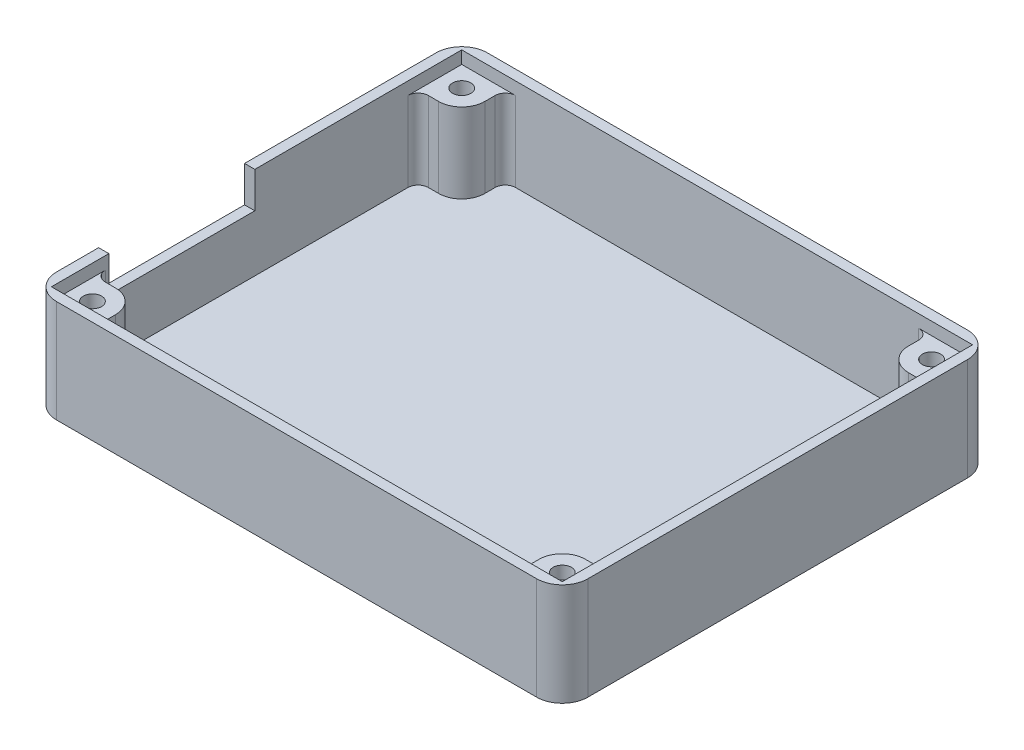
SolidWorks part; units mm, degrees
ref_plane "Front Plane" through (0, 0, 0) normal (0, 0, 1) x (1, 0, 0)
ref_plane "Top Plane" through (0, 0, 0) normal (0, 1, 0) x (1, 0, 0)
ref_plane "Right Plane" through (0, 0, 0) normal (1, 0, 0) x (0, 0, -1)
sketch "Sketch1" plane through (0, 0, 0) normal (0, 1, 0) x (1, 0, 0)
  line L0 (-36.1611, 34.3606) -> (-36.1611, -16.4394) construction
  line L1 (-38.7011, 34.3606) -> (24.5449, 34.3606)
  line L2 (-38.7011, 34.3606) -> (-38.7011, -16.4394)
  line L3 (-38.7011, -16.4394) -> (24.5449, -16.4394)
  line L4 (24.5449, 34.3606) -> (24.5449, -16.4394)
  line L5 (-38.7011, 31.8206) -> (24.5449, 31.8206) construction
  line L6 (22.0049, 34.3606) -> (22.0049, -16.4394) construction
  line L7 (-38.7011, -13.8994) -> (24.5449, -13.8994) construction
  line L8 (-7.0781, 31.8206) -> (-7.0781, -13.8994) construction
  line L9 (22.0049, 8.9606) -> (-36.1611, 8.9606) construction
  dimension "D1" = 63.246
  dimension "D2" = 50.8
  dimension "D3" = 2.54
  dimension "D4" = 2.54
  dimension "D5" = 2.54
  dimension "D6" = 2.54
sketch "Sketch4" plane through (0, 0, 0) normal (0, 1, 0) x (1, 0, 0)
  line L0 (-34.6003, 169.5077) -> (28.6457, 169.5077) construction
  dimension "D1" = 63.246
sketch "Sketch5" plane through (0, 0, 0) normal (0, 1, 0) x (1, 0, 0)
  line L8 (25.8149, -17.7094) -> (25.8149, 35.6306)
  line L9 (25.8149, 35.6306) -> (-39.9711, 35.6306)
  line L10 (-39.9711, 35.6306) -> (-39.9711, -17.7094)
  line L11 (-39.9711, -17.7094) -> (25.8149, -17.7094)
  line L12 (25.8149, -17.7094) -> (25.8149, 35.6306)
  line L13 (25.8149, 35.6306) -> (-39.9711, 35.6306)
  line L14 (-39.9711, 35.6306) -> (-39.9711, -17.7094)
  line L15 (-39.9711, -17.7094) -> (25.8149, -17.7094)
  dimension "D1" = 1.27
extrude "Boss-Extrude1" add sketch "Sketch5" along normal blind 12.7
sketch "Sketch7" plane through (0, 0, 0) normal (0, -1, 0) x (1, 0, 0)
  line L0 (-38.7011, -34.3606) -> (24.5449, -34.3606) construction
  line L1 (-38.7011, -34.3606) -> (-38.7011, 16.4394) construction
  line L2 (-38.7011, 16.4394) -> (24.5449, 16.4394) construction
  line L3 (24.5449, -34.3606) -> (24.5449, 16.4394) construction
  line L4 (-32.0336, -34.3606) -> (17.8774, -34.3606)
  line L5 (-38.7011, -27.6931) -> (-38.7011, 9.7719)
  line L6 (-32.0336, 16.4394) -> (17.8774, 16.4394)
  line L7 (24.5449, -27.6931) -> (24.5449, 9.7719)
  line L8 (-33.3036, 13.8994) -> (-33.3036, 15.1694)
  line L9 (-36.1611, 11.0419) -> (-37.4311, 11.0419)
  line L10 (-36.1611, -34.3606) -> (-36.1611, 16.4394) construction
  line L11 (-38.7011, 13.8994) -> (24.5449, 13.8994) construction
  line L12 (-38.7011, 13.8994) -> (24.5449, 13.8994) construction
  line L13 (-36.1611, -34.3606) -> (-36.1611, 16.4394) construction
  line L14 (-7.0781, 13.8994) -> (-7.0781, -34.3606) construction
  line L15 (19.1474, 13.8994) -> (19.1474, 15.1694)
  line L16 (22.0049, 11.0419) -> (23.2749, 11.0419)
  line L17 (-36.1611, -8.9606) -> (22.5409, -8.9606) construction
  line L18 (22.0049, -28.9631) -> (23.2749, -28.9631)
  line L19 (19.1474, -31.8206) -> (19.1474, -33.0906)
  line L20 (-33.3036, -31.8206) -> (-33.3036, -33.0906)
  line L21 (-36.1611, -28.9631) -> (-37.4311, -28.9631)
  circle A0 centre (-36.1611, 13.8994) radius 1.5875 construction
  arc A1 (-36.1611, 11.0419) -> (-33.3036, 13.8994) centre (-36.1611, 13.8994) ccw
  arc A2 (-38.7011, 9.7719) -> (-37.4311, 11.0419) centre (-37.4311, 9.7719) cw
  circle A3 centre (-36.1611, 13.8994) radius 2.8575 construction
  arc A4 (-33.3036, 15.1694) -> (-32.0336, 16.4394) centre (-32.0336, 15.1694) cw
  arc A5 (19.1474, 15.1694) -> (17.8774, 16.4394) centre (17.8774, 15.1694) ccw
  arc A6 (22.0049, 11.0419) -> (19.1474, 13.8994) centre (22.0049, 13.8994) cw
  arc A7 (24.5449, 9.7719) -> (23.2749, 11.0419) centre (23.2749, 9.7719) ccw
  arc A8 (24.5449, -27.6931) -> (23.2749, -28.9631) centre (23.2749, -27.6931) cw
  arc A9 (22.0049, -28.9631) -> (19.1474, -31.8206) centre (22.0049, -31.8206) ccw
  arc A10 (19.1474, -33.0906) -> (17.8774, -34.3606) centre (17.8774, -33.0906) cw
  arc A11 (-33.3036, -33.0906) -> (-32.0336, -34.3606) centre (-32.0336, -33.0906) ccw
  arc A12 (-36.1611, -28.9631) -> (-33.3036, -31.8206) centre (-36.1611, -31.8206) cw
  arc A13 (-38.7011, -27.6931) -> (-37.4311, -28.9631) centre (-37.4311, -27.6931) ccw
  point P12 (-33.371, 13.8931)
  dimension "D1" = 3.175
  dimension "D3" = 1.27
  dimension "D4" = 1.27
  dimension "D2" = 1.27
extrude "Cut-Extrude1" cut sketch "Sketch7" against normal blind 11.43
fillet "Fillet1" radius 3.175 4 edges at (-39.9711, 6.35, -35.6306) (25.8149, 6.35, -35.6306) (25.8149, 6.35, 17.7094) (-39.9711, 6.35, 17.7094)
sketch "Sketch8" plane through (0, 0, 0) normal (0, 1, 0) x (1, 0, 0)
  line L0 (-38.7011, 34.3606) -> (-38.7011, -16.4394) construction
  line L1 (-38.7011, -16.4394) -> (24.5449, -16.4394) construction
  line L2 (-38.7011, 34.3606) -> (24.5449, 34.3606) construction
  line L3 (24.5449, 34.3606) -> (24.5449, -16.4394) construction
  line L4 (-38.7011, 34.3606) -> (-38.7011, -16.4394)
  line L5 (-38.7011, -16.4394) -> (24.5449, -16.4394)
  line L6 (-38.7011, 34.3606) -> (24.5449, 34.3606)
  line L7 (24.5449, 34.3606) -> (24.5449, -16.4394)
extrude "Cut-Extrude2" cut sketch "Sketch8" along normal blind 1.5621
sketch "Sketch9" plane through (0, 0, 0) normal (0, 1, 0) x (1, 0, 0)
  line L0 (-38.7011, -16.4394) -> (24.5449, -16.4394) construction
  line L1 (34.2125, -9.3274) -> (18.9109, -9.3274)
  line L2 (34.2125, -9.3274) -> (34.2125, 8.7429)
  line L3 (34.2125, 8.7429) -> (18.9109, 8.7429)
  line L4 (18.9109, -9.3274) -> (18.9109, 8.7429)
  line L5 (-38.7011, -16.4394) -> (24.5449, -16.4394) construction
  dimension "D1" = 18.0703
  dimension "D2" = 15.3016
  dimension "D3" = 7.112
extrude "Cut-Extrude3" cut sketch "Sketch9" along normal blind 4.445
hole_wizard "Tap Drill for #4-40 Tap1" positions "Sketch11" profile "Sketch10" hole size "#4-40" standard "ANSI Inch"
sketch "Sketch11" plane through (0, 0, 0) normal (0, -1, 0) x (-1, 0, 0)
  line L1 (36.1611, 34.3606) -> (36.1611, -16.4394) construction
  line L2 (38.7011, -13.8994) -> (-24.5449, -13.8994) construction
  line L3 (36.1611, 34.3606) -> (36.1611, -16.4394) construction
  line L4 (38.7011, -13.8994) -> (-24.5449, -13.8994) construction
  point P12 (36.1611, -13.8994)
sketch "Sketch10" plane through (-36.1611, 0, 13.8994) normal (1, 0, 0) x (0, 0, -1)
  line L0 (0, 0) -> (0, 9.5692)
  line L1 (0, 9.5692) -> (1.1303, 8.89)
  line L2 (1.1303, 8.89) -> (1.1303, 0)
  line L5 (1.1303, 0) -> (0, 0)
  line L10 (0, 9.5692) -> (-1.1303, 8.89) construction
  line L11 (0, -6.35) -> (0, 107.95) construction
  dimension "Hole Dia." = 2.2606
  dimension "Hole Depth" = 8.89
  dimension "Drill Angle" = 118
ref_plane "Plane2" through (-7.0781, 0, 0) normal (1, 0, 0) x (0, 0, 1)
ref_plane "Plane3" through (0, 0, -8.9606) normal (0, 0, 1) x (-1, 0, 0)
mirror "Mirror1" about plane through (-7.0781, 0, 0) normal (1, 0, 0) of "Tap Drill for #4-40 Tap1"
mirror "Mirror2" about plane through (0, 0, -8.9606) normal (0, 0, 1) of "Mirror1", "Tap Drill for #4-40 Tap1"
sketch3d "3DSketch1"
  point P0 (-11.0047, 12.7, -22.1233)
move or copy body "Body-Move/Copy1" bodies to move or copy 107 copy no rotation origin (-7.0781, 6.35, 0) rotation axis (0, 0, 1) rotation angle 180
